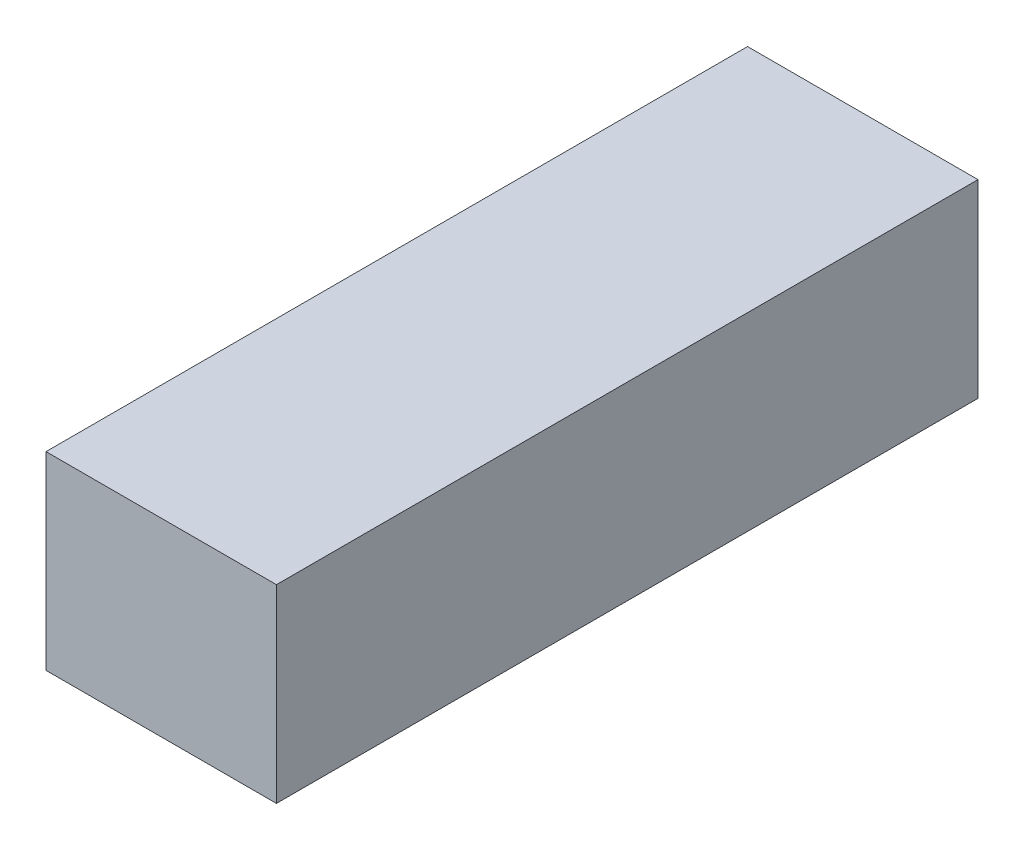
SolidWorks part; units mm, degrees
ref_plane "Front Plane" through (0, 0, 0) normal (0, 0, 1) x (1, 0, 0)
ref_plane "Top Plane" through (0, 0, 0) normal (0, 1, 0) x (1, 0, 0)
ref_plane "Right Plane" through (0, 0, 0) normal (1, 0, 0) x (0, 0, -1)
sketch "Sketch1" plane through (0, 0, 0) normal (0, 0, 1) x (1, 0, 0)
  line L1 (-22.5, 18.5) -> (22.5, 18.5)
  line L2 (-22.5, 18.5) -> (-22.5, -18.5)
  line L3 (-22.5, -18.5) -> (22.5, -18.5)
  line L4 (22.5, 18.5) -> (22.5, -18.5)
  line L5 (-22.5, 18.5) -> (22.5, -18.5) construction
  line L6 (-22.5, -18.5) -> (22.5, 18.5) construction
  point P0 (0, 0)
  dimension "D1" = 45
  dimension "D2" = 37
extrude "Boss-Extrude1" add sketch "Sketch1" along normal blind 137
